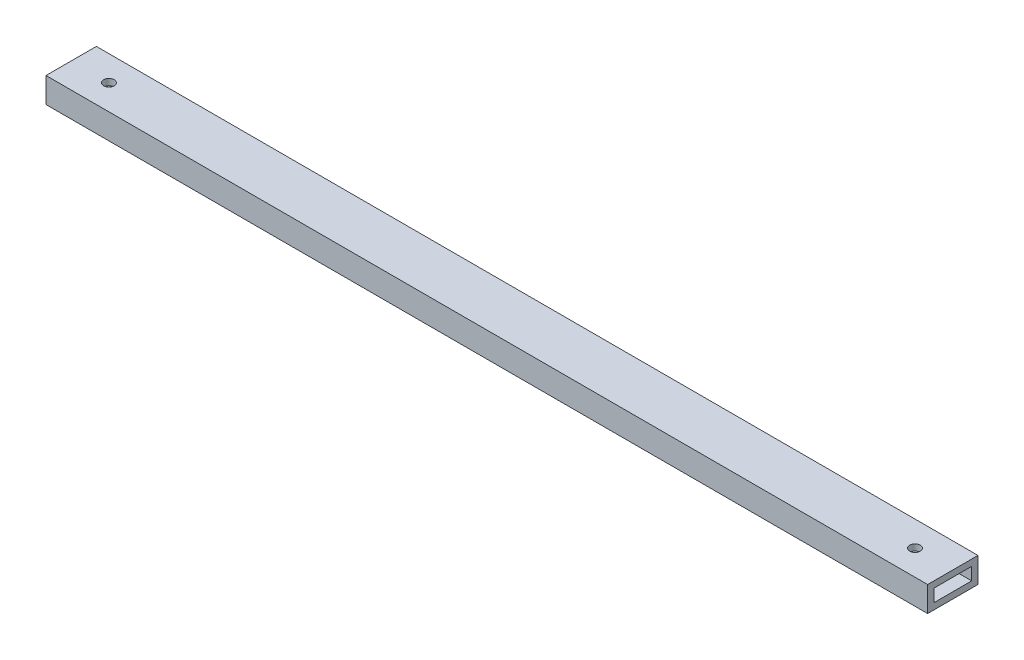
SolidWorks part; units mm, degrees
ref_plane "Front" through (0, 0, 0) normal (0, 0, 1) x (1, 0, 0)
ref_plane "Top" through (0, 0, 0) normal (0, 1, 0) x (1, 0, 0)
ref_plane "Right" through (0, 0, 0) normal (1, 0, 0) x (0, 0, -1)
sketch "Sketch1" plane through (0, 0, 0) normal (1, 0, 0) x (0, 0, -1)
  line L0 (3.175, 3.175) -> (22.225, 3.175)
  line L1 (0, 0) -> (25.4, 0)
  line L2 (0, 0) -> (0, 12.7)
  line L3 (0, 12.7) -> (25.4, 12.7)
  line L4 (25.4, 0) -> (25.4, 12.7)
  line L5 (22.225, 3.175) -> (22.225, 9.525)
  line L6 (3.175, 9.525) -> (22.225, 9.525)
  line L7 (3.175, 3.175) -> (3.175, 9.525)
  dimension "D1" = 12.7
  dimension "D2" = 25.4
  dimension "D3" = 3.175
extrude "Boss-Extrude1" add sketch "Sketch1" along normal blind 444.5
sketch "Sketch2" plane through (0, 12.7, 0) normal (0, 1, 0) x (1, 0, 0)
  line L0 (0, 12.7) -> (19.05, 12.7) construction
  line L1 (0, 25.4) -> (0, 0) construction
  line L2 (222.25, 25.4) -> (222.25, 0) construction
  line L3 (444.5, 25.4) -> (0, 25.4) construction
  line L4 (444.5, 0) -> (0, 0) construction
  circle A0 centre (19.05, 12.7) radius 2.667
  circle A1 centre (425.45, 12.7) radius 2.667
  dimension "D1" = 19.05
extrude "Cut-Extrude1" cut sketch "Sketch2" against normal through all
